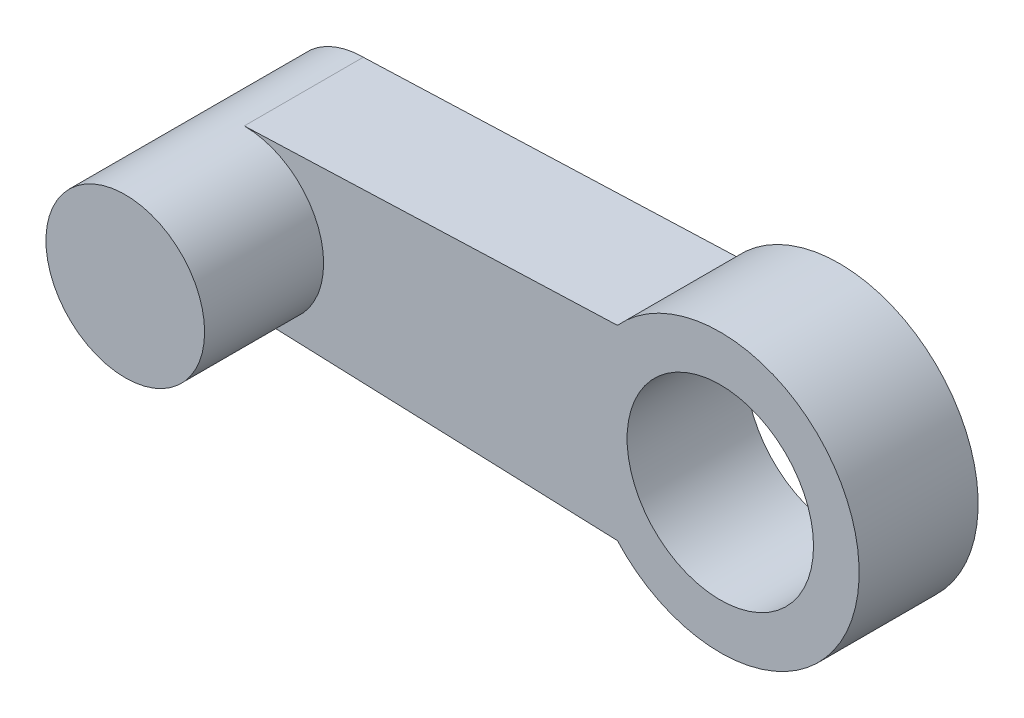
SolidWorks part; units mm, degrees
ref_plane "Front Plane" through (0, 0, 0) normal (0, 0, 1) x (1, 0, 0)
ref_plane "Top Plane" through (0, 0, 0) normal (0, 1, 0) x (1, 0, 0)
ref_plane "Right Plane" through (0, 0, 0) normal (1, 0, 0) x (0, 0, -1)
sketch "Sketch1" plane through (0, 0, 0) normal (0, 0, 1) x (1, 0, 0)
  line L4 (-10.9395, 2) -> (-1.5333, 2.35)
  line L5 (-10.9395, -2) -> (-1.5333, -2.35)
  circle A1 centre (1.0605, 0) radius 3.5
  circle A2 centre (-10.9395, 0) radius 2
  circle A3 centre (1.0605, 0) radius 2.35
  dimension "D2" = 7
  dimension "D6" = 4
  dimension "D1" = 4.7
  dimension "D5" = 4.7
  dimension "D7" = 12
  dimension "D8" = 9.4063
extrude "Boss-Extrude1" add sketch "Sketch1" along normal blind 3 contours A2 L5 A1 L4 | A1 | A2
sketch "Sketch2" plane through (0, 0, 3) normal (0, 0, 1) x (1, 0, 0)
  circle A1 centre (-10.9395, 0) radius 2
extrude "Boss-Extrude2" add sketch "Sketch2" along normal blind 3
